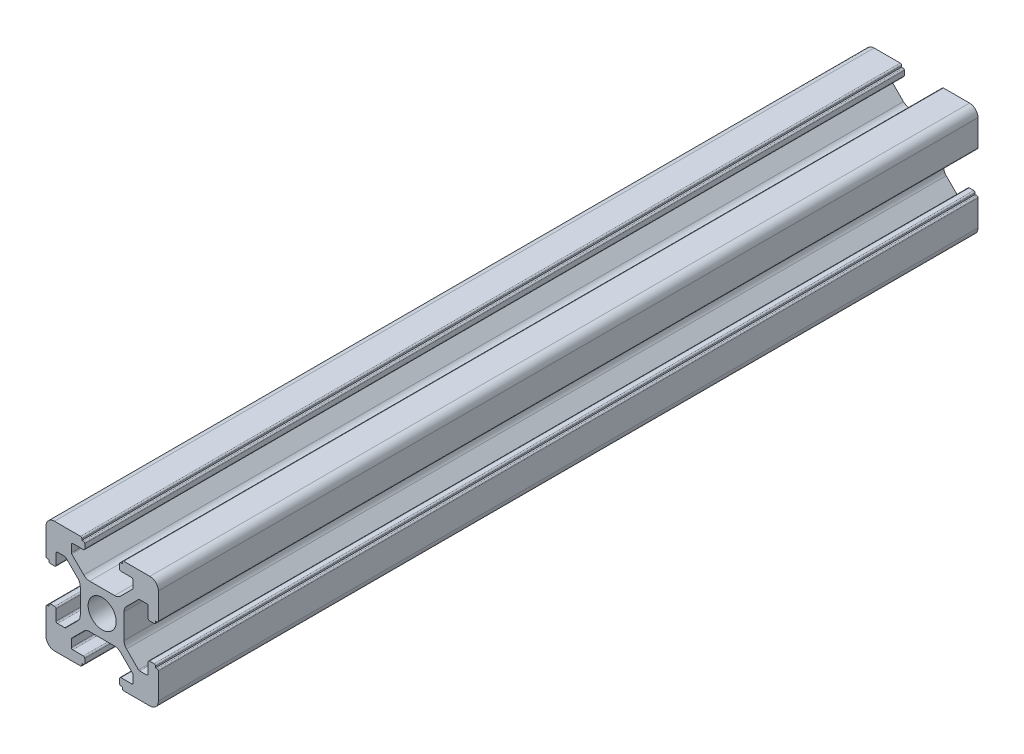
SolidWorks part; units mm, degrees
ref_plane "前视基准面" through (0, 0, 0) normal (0, 0, 1) x (1, 0, 0)
ref_plane "上视基准面" through (0, 0, 0) normal (0, 1, 0) x (1, 0, 0)
ref_plane "右视基准面" through (0, 0, 0) normal (1, 0, 0) x (0, 0, -1)
sketch "草图1" plane through (0, 0, 0) normal (0, 0, 1) x (1, 0, 0)
  line L0 (0, 0) -> (0, 5.5) construction
  line L1 (-8.5023, -10.0023) -> (-3.85, -10.0023)
  line L2 (-10.0023, -8.5023) -> (-10.0023, -3.85)
  line L3 (-8.5023, 10.0023) -> (-3.85, 10.0023)
  line L4 (10.0023, -8.5023) -> (10.0023, -3.85)
  line L5 (-10.0023, -10.0023) -> (10.0023, 10.0023) construction
  line L6 (-10.0023, 10.0023) -> (10.0023, -10.0023) construction
  line L7 (-2.218, -3.9) -> (2.218, -3.9)
  line L8 (-3.9, -2.218) -> (-3.9, 2.218)
  line L9 (-2.218, 3.9) -> (2.218, 3.9)
  line L10 (3.9, -2.218) -> (3.9, 2.218)
  line L11 (-3.9, -3.9) -> (3.9, 3.9) construction
  line L12 (-3.9, 3.9) -> (3.9, -3.9) construction
  line L13 (-5.25, -8.2) -> (-3.35, -8.2)
  line L14 (-8.2, -5.25) -> (-8.2, -3.35)
  line L15 (-5.25, 8.2) -> (-3.35, 8.2)
  line L16 (8.2, -5.25) -> (8.2, -3.35)
  line L17 (-8.2, -8.2) -> (8.2, 8.2) construction
  line L18 (-8.2, 8.2) -> (8.2, -8.2) construction
  line L19 (-7.95, 5.5) -> (-6.6642, 5.5)
  line L20 (0, 0) -> (5.5, 0) construction
  line L23 (-5.5, 7.95) -> (-5.5, 6.6642)
  line L26 (0, 0) -> (-0.5303, 0.5303)
  line L27 (3.2787, 4.3393) -> (5.4268, 6.4874)
  line L28 (0, 0) -> (0.5303, -0.5303)
  line L29 (5.5, 6.6642) -> (5.5, 7.95)
  line L30 (4.3393, 3.2787) -> (6.4874, 5.4268)
  line L31 (6.6642, 5.5) -> (7.95, 5.5)
  line L32 (4.3393, -3.2787) -> (6.4874, -5.4268)
  line L33 (3.2787, -4.3393) -> (5.4268, -6.4874)
  line L34 (-3.2787, -4.3393) -> (-5.4268, -6.4874)
  line L35 (-4.3393, -3.2787) -> (-6.4874, -5.4268)
  line L36 (-4.3393, 3.2787) -> (-6.4874, 5.4268)
  line L37 (-3.2787, 4.3393) -> (-5.4268, 6.4874)
  line L38 (3.1, -8.45) -> (3.1, -9.2523)
  line L39 (8.45, 3.1) -> (9.2523, 3.1)
  line L40 (-5.5, -6.6642) -> (-5.5, -7.95)
  line L41 (-6.6642, -5.5) -> (-7.95, -5.5)
  line L42 (5.5, -6.6642) -> (5.5, -7.95)
  line L43 (6.6642, -5.5) -> (7.95, -5.5)
  line L44 (9.2523, -3.1) -> (8.45, -3.1)
  line L46 (10.0023, 3.85) -> (10.0023, 8.5023)
  line L47 (8.2, 3.35) -> (8.2, 5.25)
  line L48 (-3.1, -9.2523) -> (-3.1, -8.45)
  line L49 (-8.45, -3.1) -> (-9.2523, -3.1)
  line L50 (-9.2523, 3.1) -> (-8.45, 3.1)
  line L51 (-3.1, 8.45) -> (-3.1, 9.2523)
  line L52 (3.1, 9.2523) -> (3.1, 8.45)
  line L53 (3.85, 10.0023) -> (8.5023, 10.0023)
  line L54 (3.35, 8.2) -> (5.25, 8.2)
  line L55 (-10.0023, 3.85) -> (-10.0023, 8.5023)
  line L56 (-8.2, 3.35) -> (-8.2, 5.25)
  line L57 (3.35, -8.2) -> (5.25, -8.2)
  line L58 (3.85, -10.0023) -> (8.5023, -10.0023)
  line L59 (9.7523, -3.6) -> (9.5023, -3.6)
  line L61 (9.7523, 3.6) -> (9.5023, 3.6)
  line L62 (9.5023, -3.6) -> (9.5023, -3.35)
  line L63 (3.6, -9.7523) -> (3.6, -9.5023)
  line L64 (3.35, -9.5023) -> (3.6, -9.5023)
  line L65 (9.5023, 3.35) -> (9.5023, 3.6)
  line L66 (-3.6, -9.5023) -> (-3.35, -9.5023)
  line L67 (-3.6, -9.7523) -> (-3.6, -9.5023)
  line L68 (-9.7523, -3.6) -> (-9.5023, -3.6)
  line L69 (-9.5023, -3.35) -> (-9.5023, -3.6)
  line L70 (-9.5023, 3.6) -> (-9.5023, 3.35)
  line L71 (-9.7523, 3.6) -> (-9.5023, 3.6)
  line L72 (-3.6, 9.7523) -> (-3.6, 9.5023)
  line L73 (-3.35, 9.5023) -> (-3.6, 9.5023)
  line L74 (3.6, 9.5023) -> (3.35, 9.5023)
  line L75 (3.6, 9.7523) -> (3.6, 9.5023)
  circle A0 centre (0, 0) radius 2.5
  arc A1 (10.0023, 8.5023) -> (8.5023, 10.0023) centre (8.5023, 8.5023) ccw
  arc A2 (8.5023, -10.0023) -> (10.0023, -8.5023) centre (8.5023, -8.5023) ccw
  arc A3 (-10.0023, -8.5023) -> (-8.5023, -10.0023) centre (-8.5023, -8.5023) ccw
  arc A4 (-10.0023, 8.5023) -> (-8.5023, 10.0023) centre (-8.5023, 8.5023) cw
  arc A5 (-9.5023, -3.35) -> (-9.2523, -3.1) centre (-9.2523, -3.35) cw
  arc A6 (-9.7523, -3.6) -> (-10.0023, -3.85) centre (-9.7523, -3.85) ccw
  arc A7 (-8.45, -3.1) -> (-8.2, -3.35) centre (-8.45, -3.35) cw
  arc A8 (-7.95, -5.5) -> (-8.2, -5.25) centre (-7.95, -5.25) cw
  arc A9 (-6.4874, -5.4268) -> (-6.6642, -5.5) centre (-6.6642, -5.25) cw
  arc A10 (-5.4268, -6.4874) -> (-5.5, -6.6642) centre (-5.25, -6.6642) ccw
  arc A11 (-5.5, -7.95) -> (-5.25, -8.2) centre (-5.25, -7.95) ccw
  arc A12 (-3.6, -9.7523) -> (-3.85, -10.0023) centre (-3.85, -9.7523) cw
  arc A13 (-3.35, -9.5023) -> (-3.1, -9.2523) centre (-3.35, -9.2523) ccw
  arc A14 (-3.1, -8.45) -> (-3.35, -8.2) centre (-3.35, -8.45) ccw
  arc A15 (3.1, -8.45) -> (3.35, -8.2) centre (3.35, -8.45) cw
  arc A16 (5.5, -7.95) -> (5.25, -8.2) centre (5.25, -7.95) cw
  arc A17 (5.4268, -6.4874) -> (5.5, -6.6642) centre (5.25, -6.6642) cw
  arc A18 (6.4874, -5.4268) -> (6.6642, -5.5) centre (6.6642, -5.25) ccw
  arc A19 (7.95, -5.5) -> (8.2, -5.25) centre (7.95, -5.25) ccw
  arc A20 (8.45, -3.1) -> (8.2, -3.35) centre (8.45, -3.35) ccw
  arc A21 (9.5023, -3.35) -> (9.2523, -3.1) centre (9.2523, -3.35) ccw
  arc A22 (9.7523, -3.6) -> (10.0023, -3.85) centre (9.7523, -3.85) cw
  arc A23 (3.35, -9.5023) -> (3.1, -9.2523) centre (3.35, -9.2523) cw
  arc A24 (3.6, -9.7523) -> (3.85, -10.0023) centre (3.85, -9.7523) ccw
  arc A25 (7.95, 5.5) -> (8.2, 5.25) centre (7.95, 5.25) cw
  arc A26 (8.2, 3.35) -> (8.45, 3.1) centre (8.45, 3.35) ccw
  arc A27 (9.5023, 3.35) -> (9.2523, 3.1) centre (9.2523, 3.35) cw
  arc A28 (9.7523, 3.6) -> (10.0023, 3.85) centre (9.7523, 3.85) ccw
  arc A29 (6.6642, 5.5) -> (6.4874, 5.4268) centre (6.6642, 5.25) ccw
  arc A30 (5.4268, 6.4874) -> (5.5, 6.6642) centre (5.25, 6.6642) ccw
  arc A31 (5.5, 7.95) -> (5.25, 8.2) centre (5.25, 7.95) ccw
  arc A32 (3.1, 8.45) -> (3.35, 8.2) centre (3.35, 8.45) ccw
  arc A33 (3.6, 9.7523) -> (3.85, 10.0023) centre (3.85, 9.7523) cw
  arc A34 (3.35, 9.5023) -> (3.1, 9.2523) centre (3.35, 9.2523) ccw
  arc A35 (-9.7523, 3.6) -> (-10.0023, 3.85) centre (-9.7523, 3.85) cw
  arc A36 (-9.5023, 3.35) -> (-9.2523, 3.1) centre (-9.2523, 3.35) ccw
  arc A37 (-8.45, 3.1) -> (-8.2, 3.35) centre (-8.45, 3.35) ccw
  arc A38 (-8.2, 5.25) -> (-7.95, 5.5) centre (-7.95, 5.25) cw
  arc A39 (-6.4874, 5.4268) -> (-6.6642, 5.5) centre (-6.6642, 5.25) ccw
  arc A40 (-5.4268, 6.4874) -> (-5.5, 6.6642) centre (-5.25, 6.6642) cw
  arc A41 (-5.5, 7.95) -> (-5.25, 8.2) centre (-5.25, 7.95) cw
  arc A42 (-3.1, 8.45) -> (-3.35, 8.2) centre (-3.35, 8.45) cw
  arc A43 (-3.1, 9.2523) -> (-3.35, 9.5023) centre (-3.35, 9.2523) ccw
  arc A44 (-3.6, 9.7523) -> (-3.85, 10.0023) centre (-3.85, 9.7523) ccw
  arc A45 (-4.3393, 3.2787) -> (-3.9, 2.218) centre (-5.4, 2.218) cw
  arc A46 (-3.2787, 4.3393) -> (-2.218, 3.9) centre (-2.218, 5.4) ccw
  arc A47 (3.2787, 4.3393) -> (2.218, 3.9) centre (2.218, 5.4) cw
  arc A48 (4.3393, 3.2787) -> (3.9, 2.218) centre (5.4, 2.218) ccw
  arc A49 (4.3393, -3.2787) -> (3.9, -2.218) centre (5.4, -2.218) cw
  arc A50 (3.2787, -4.3393) -> (2.218, -3.9) centre (2.218, -5.4) ccw
  arc A51 (-4.3393, -3.2787) -> (-3.9, -2.218) centre (-5.4, -2.218) ccw
  arc A52 (-2.218, -3.9) -> (-3.2787, -4.3393) centre (-2.218, -5.4) ccw
  point P0 (0, 0)
  point P7 (10.0023, 0)
  point P62 (0, 0)
  point P76 (0, 0)
  point P92 (-8.2, -5.5)
  point P99 (0, 0)
  point P106 (-5.5, -8.2)
  point P117 (5.5, -8.2)
  point P124 (8.2, -5.5)
  point P137 (8.2, 5.5)
  point P140 (8.2, 3.1)
  point P147 (6.5607, 5.5)
  point P152 (5.5, 8.2)
  point P167 (-8.2, 5.5)
  point P174 (-5.5, 8.2)
  dimension "D1" = 1.5
  dimension "D5" = 0.25
  dimension "D6" = 1.5
  dimension "D2" = 4
  dimension "D3" = 4
  dimension "D4" = 4
extrude "凸台-拉伸1" add sketch "草图1" along normal blind 1220 contours A52 L7 A50 L33 A17 L42 A16 L57 A15 L38 A23 L64 L63 A24 L58 A2 L4 A22 L59 L62 A21 L44 A20 L16 A19 L43 A18 L32 A49 L10 A48 L30 A29 L31 A25 L47 A26 L39 A27 L65 L61 A28 L46 A1 L53 A33 L75 L74 A34 L52 A32
ref_plane "Plane1" through (0, 0, 1074) normal (0, 0, 1) x (1, 0, 0)
sketch "Sketch1" plane through (0, 0, 1074) normal (0, 0, 1) x (1, 0, 0)
  circle A0 centre (0, 0) radius 16.7715
extrude "Cut-Extrude1" cut sketch "Sketch1" against normal through all
ref_plane "CenterPlane" through (0, 0, 1147) normal (0, 0, 1) x (1, 0, 0)
